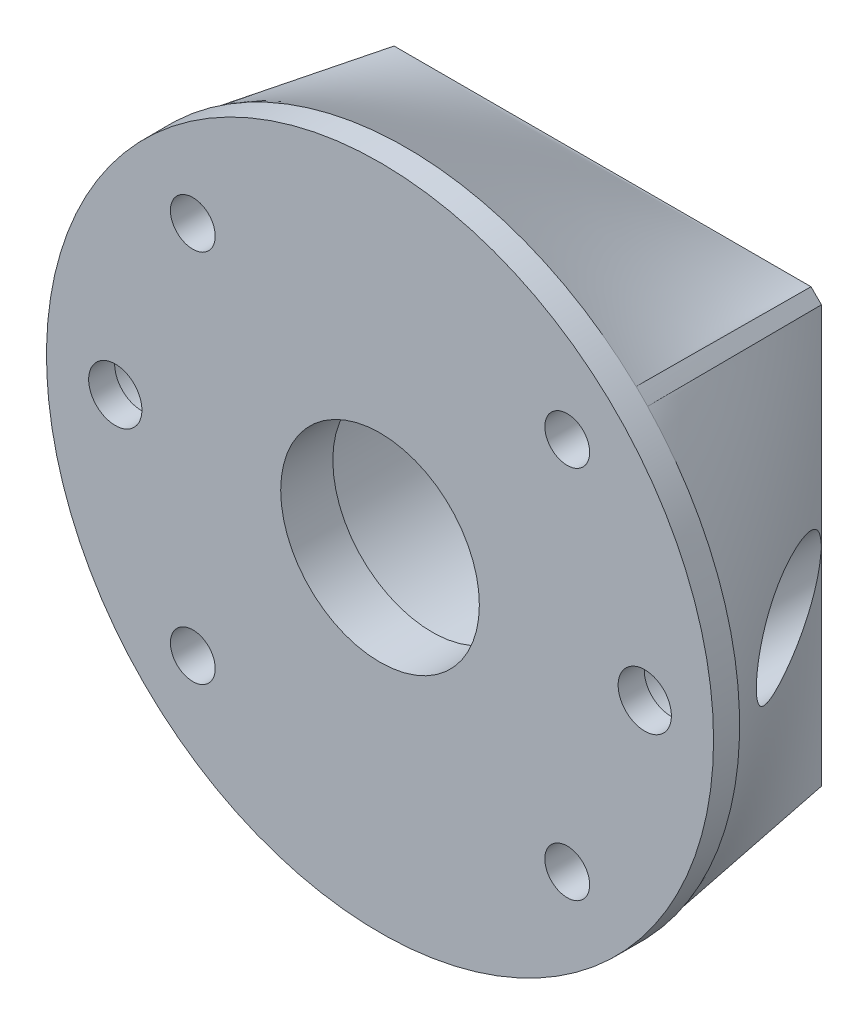
SolidWorks part; units mm, degrees
ref_plane "Front Plane" through (0, 0, 0) normal (0, 0, 1) x (1, 0, 0)
ref_plane "Top Plane" through (0, 0, 0) normal (0, 1, 0) x (1, 0, 0)
ref_plane "Right Plane" through (0, 0, 0) normal (1, 0, 0) x (0, 0, -1)
sketch "Sketch1" plane through (0, 0, 0) normal (0, 0, 1) x (1, 0, 0)
  circle A0 centre (0, 0) radius 32
  dimension "D1" = 64
sketch3d "3DSketch1"
  line L0 (0, 0, 0) -> (0, 0, -18.85) construction
  dimension "D1" = 18.85
ref_plane "Plane1" through (0, 0, -18.85) normal (0, 0, -1) x (-1, 0, 0)
sketch "Sketch2" plane through (0, 0, -18.85) normal (0, 0, -1) x (-1, 0, 0)
  line L0 (0, 0) -> (0, 21) construction
  line L7 (0, 0) -> (-21, 0) construction
  line L10 (20, 21) -> (21, 20)
  line L13 (-21, 20) -> (-20, 21)
  line L16 (-21, -20) -> (-20, -21)
  line L19 (21, -20) -> (20, -21)
  line L20 (21, -20) -> (21, 20)
  line L21 (20, -21) -> (-20, -21)
  line L22 (-21, -20) -> (-21, 20)
  line L23 (-20, 21) -> (20, 21)
  dimension "D1" = 21
  dimension "D2" = 21
loft "Loft3" add profiles "Sketch1", "Sketch2"
sketch "Sketch3" plane through (0, 0, -18.85) normal (0, 0, -1) x (-1, 0, 0)
  line L0 (0, 0) -> (25.4, 0) construction
  line L1 (0, 0) -> (0, 40) construction
  line L2 (0, 0) -> (0, -40) construction
  circle A0 centre (25.4, 0) radius 4.35
  circle A1 centre (-25.4, 0) radius 4.35
  dimension "D2" = 8.7
  dimension "D1" = 25.4
extrude "Cut-Extrude1" cut sketch "Sketch3" against normal blind 19.35
sketch "Sketch4" plane through (0, 0, 0) normal (0, 0, 1) x (1, 0, 0)
  circle A0 centre (0, 0) radius 32
  dimension "D1" = 64
extrude "Boss-Extrude1" add sketch "Sketch4" along normal blind 2.5
sketch "Sketch5" plane through (0, 0, -18.85) normal (0, 0, -1) x (-1, 0, 0)
  line L0 (0, 0) -> (0, 40) construction
  line L1 (0, 0) -> (0, -40) construction
  circle A0 centre (25.4, 0) radius 2.555
  circle A1 centre (-25.4, 0) radius 2.555
  dimension "D1" = 5.11
extrude "Cut-Extrude2" cut sketch "Sketch5" against normal blind 40
sketch "Sketch6" plane through (0, 0, -18.85) normal (0, 0, -1) x (-1, 0, 0)
  circle A0 centre (0, 0) radius 20.01
  dimension "D1" = 40.02
extrude "Cut-Extrude3" cut sketch "Sketch6" against normal blind 3.7
sketch "Sketch7" plane through (0, 0, -18.85) normal (0, 0, -1) x (-1, 0, 0)
  circle A0 centre (0, 0) radius 12.725
  dimension "D1" = 25.45
extrude "Cut-Extrude4" cut sketch "Sketch7" against normal blind 16.35
sketch "Sketch8" plane through (0, 0, -2.5) normal (0, 0, -1) x (-1, 0, 0)
  circle A0 centre (0, 0) radius 9.53
  dimension "D1" = 19.06
extrude "Cut-Extrude5" cut sketch "Sketch8" against normal blind 16.35
sketch "Sketch9" plane through (0, 0, -18.85) normal (0, 0, -1) x (-1, 0, 0)
  line L0 (0, 0) -> (-17.9605, 17.9605) construction
  line L1 (0, 0) -> (0, 40) construction
  line L2 (0, 0) -> (-40, 0) construction
  line L3 (0, 0) -> (31.8198, 31.8198) construction
  circle A0 centre (-17.9605, 17.9605) radius 2.15
  circle A1 centre (17.9605, 17.9605) radius 2.15
  circle A2 centre (-17.9605, -17.9605) radius 2.15
  circle A3 centre (17.9605, -17.9605) radius 2.15
  dimension "D2" = 4.3
  dimension "D1" = 25.4
  dimension "D3" = 40
  dimension "D4" = 40
  dimension "D5" = 45
extrude "Cut-Extrude6" cut sketch "Sketch9" against normal blind 30
